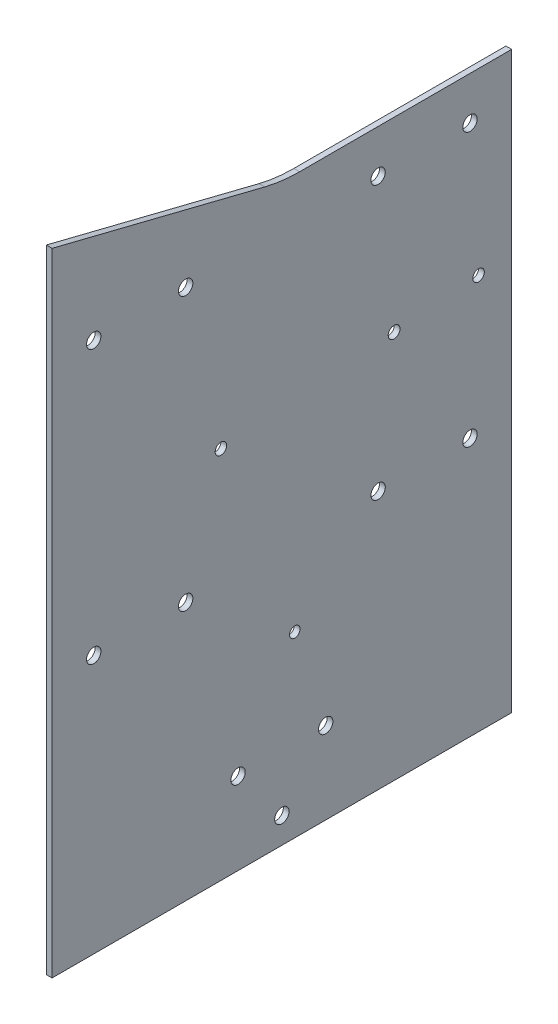
SolidWorks part; units mm, degrees
ref_plane "前视基准面" through (0, 0, 0) normal (0, 0, 1) x (1, 0, 0)
ref_plane "上视基准面" through (0, 0, 0) normal (0, 1, 0) x (1, 0, 0)
ref_plane "右视基准面" through (0, 0, 0) normal (1, 0, 0) x (0, 0, -1)
sketch "草图1" plane through (0, 0, 0) normal (1, 0, 0) x (0, 0, -1)
  line L0 (0, -93.5) -> (0, -100) construction
  line L1 (80, -100) -> (-80, -100)
  line L2 (80, -100) -> (80, 100)
  line L3 (80, 100) -> (6.1553, 100)
  line L4 (-80, -100) -> (-80, 100)
  line L5 (80, -100) -> (-80, 100) construction
  line L6 (80, 100) -> (-80, -100) construction
  line L7 (-80, 100) -> (-80, 117.4384)
  line L8 (0, 100) -> (0, 0) construction
  line L9 (-77.5149, 119.3787) -> (-5.9715, 101.4929)
  line L10 (-77.5149, 119.3787) -> (-80, 120)
  line L11 (-80, 120) -> (-80, 117.4384)
  circle A3 centre (-65.5, -10) radius 2.5
  circle A4 centre (-33.5, -10) radius 2.5
  circle A5 centre (-65.5, 85) radius 2.5
  circle A6 centre (-33.5, 85) radius 2.5
  circle A11 centre (33.5, 85) radius 2.5
  circle A12 centre (65.5, 85) radius 2.5
  circle A13 centre (33.5, -10) radius 2.5
  circle A14 centre (65.5, -10) radius 2.5
  circle A15 centre (-65.5, 180) radius 2.5 [skipped]
  circle A16 centre (-33.5, 180) radius 2.5 [skipped]
  circle A17 centre (0, -91) radius 2.5
  circle A18 centre (-15.25, -71.5) radius 2.5
  circle A19 centre (15.25, -71.5) radius 2.5
  arc A21 (6.1553, 100) -> (-5.9715, 101.4929) centre (6.1553, 150) cw
  point P0 (0, 0)
  point P26 (-80, 120)
  dimension "D3" = 5
  dimension "D4" = 5
  dimension "D5" = 5
  dimension "D6" = 30.5
  dimension "D7" = 15.25
  dimension "D8" = 9
  dimension "D9" = 28.5
  dimension "D10" = 80
  dimension "D11" = 5
  dimension "D12" = 5
  dimension "D13" = 32
  dimension "D14" = 14.5
  dimension "D16" = 90
  dimension "D19" = 50
  dimension "D1" = 160
  dimension "D2" = 200
  dimension "D17" = 20
  dimension "D15" = 3
extrude "凸台-拉伸1" add sketch "草图1" along normal blind 2
sketch "草图2" plane through (2, 0, 0) normal (1, 0, 0) x (0, 0, -1)
  line L0 (80, -100) -> (80, 100) construction
  circle A0 centre (68.4727, 37.6408) radius 2.0007
  circle A1 centre (39.0736, 35.2035) radius 2.0544
  circle A2 centre (-21.2196, 30.205) radius 2
  circle A3 centre (4.4955, -37.9033) radius 1.8475
  dimension "D1" = 11.5273
extrude "切除-拉伸1" cut sketch "草图2" against normal through all
